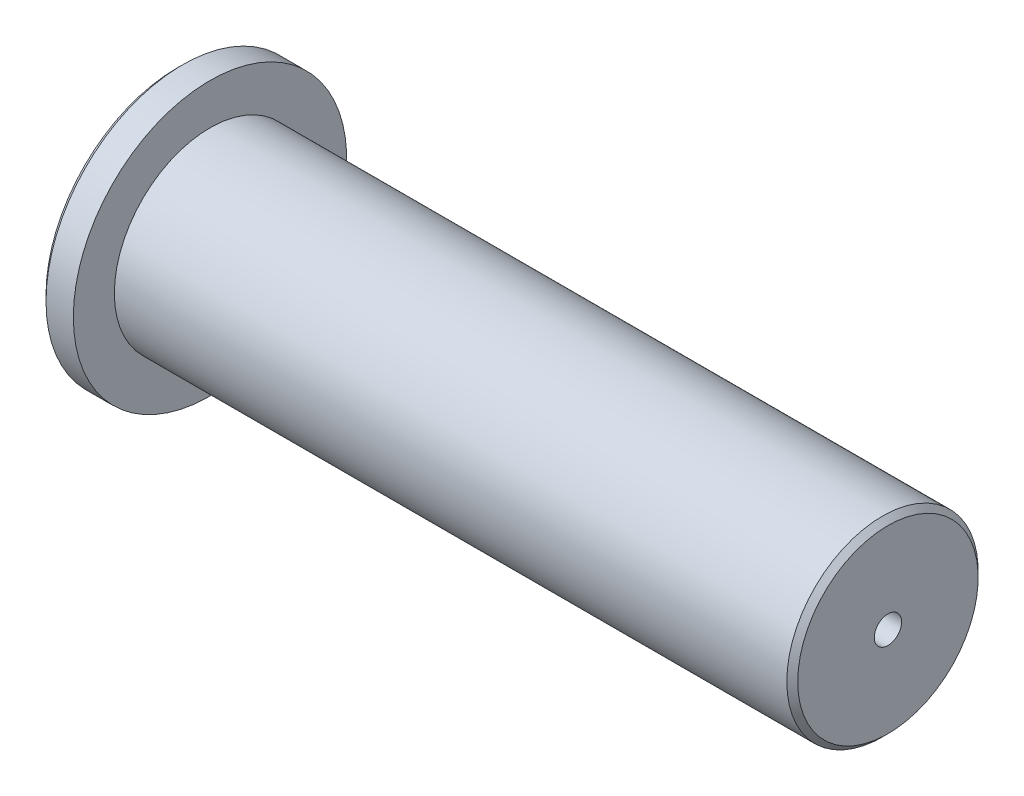
SolidWorks part; units mm, degrees
material "AISI 1045 钢，冷拔"
ref_plane "前视基准面" through (0, 0, 0) normal (0, 0, 1) x (1, 0, 0)
ref_plane "上视基准面" through (0, 0, 0) normal (0, 1, 0) x (1, 0, 0)
ref_plane "右视基准面" through (0, 0, 0) normal (1, 0, 0) x (0, 0, -1)
ref_plane "基准面4" through (0, 0, 0) normal (0, 0, 1) x (1, 0, 0)
sketch "草图1" plane through (0, 0, 0) normal (0, 0, 1) x (1, 0, 0)
  line L0 (-4215.7186, -7413.9832) -> (-4110.5756, -7413.9832) construction
  line L3 (-4236.1784, -7413.9832) -> (-4106.1784, -7413.9832)
  line L4 (-4230.1784, -7396.4832) -> (-4107.1784, -7396.4832)
  line L7 (-4106.1784, -7397.4832) -> (-4106.1784, -7413.9832)
  line L10 (-4235.1784, -7388.9832) -> (-4236.1784, -7389.9832)
  line L12 (-4230.1784, -7396.4832) -> (-4230.1784, -7388.9832)
  line L13 (-4230.1784, -7388.9832) -> (-4235.1784, -7388.9832)
  line L14 (-4236.1784, -7413.9832) -> (-4236.1784, -7389.9832)
  line L15 (-4107.1784, -7396.4832) -> (-4106.1784, -7397.4832)
  point P9 (-4106.1784, -7396.4832)
  point P16 (-4236.1784, -7388.9832)
  dimension "D1" = 17.5
  dimension "D2" = 6
  dimension "D3" = 25
  dimension "D4" = 130
revolve "旋转1" add sketch "草图1" angle 360 about L0
hole_wizard "M6 螺纹孔的螺纹孔钻头1" positions "草图2" profile "草图3" hole size "M6" standard "GB"
sketch "草图2" plane through (-4106.1784, 0, 0) normal (1, 0, 0) x (0, 0, -1)
  point P0 (0, -7413.9832)
sketch "草图3" plane through (-4106.1784, -7413.9832, 0) normal (0, 1, 0) x (0, 0, -1)
  line L0 (0, 0) -> (0, 16.5022)
  line L1 (0, 16.5022) -> (2.5, 15)
  line L2 (2.5, 15) -> (2.5, 0)
  line L5 (2.5, 0) -> (0, 0)
  line L10 (0, 16.5022) -> (-2.5, 15) construction
  line L11 (0, -6.35) -> (0, 107.95) construction
  dimension "孔直径" = 5
  dimension "孔深度" = 15
  dimension "导头角度" = 118
